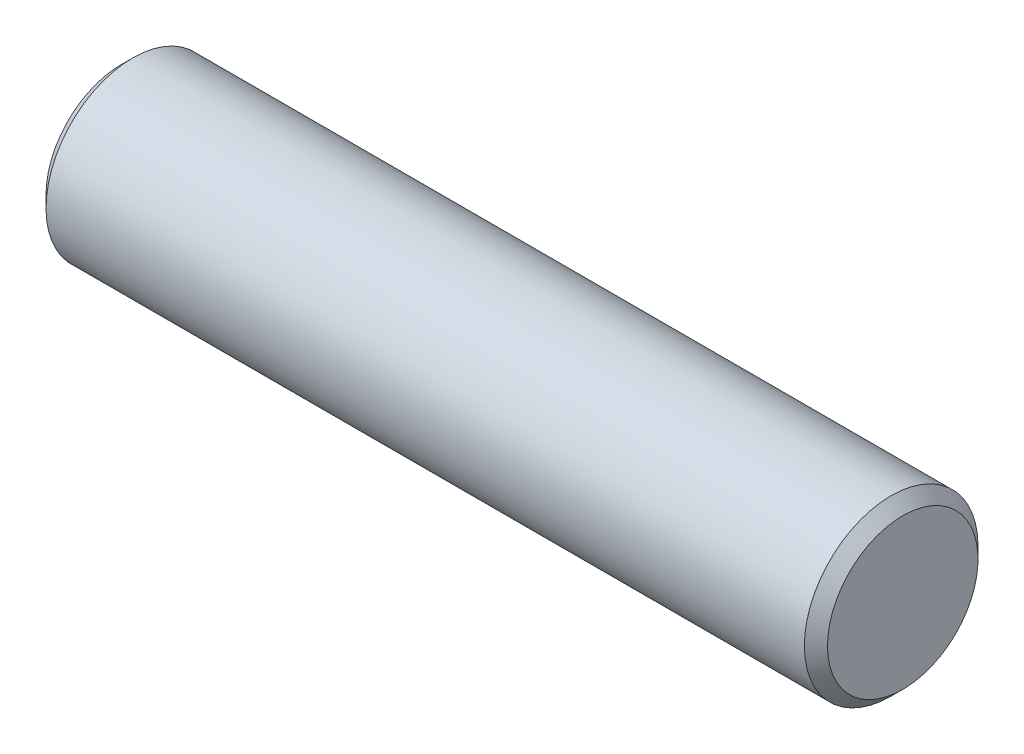
SolidWorks part; units mm, degrees
ref_plane "Front Plane" through (0, 0, 0) normal (0, 0, 1) x (1, 0, 0)
ref_plane "Top Plane" through (0, 0, 0) normal (0, 1, 0) x (1, 0, 0)
ref_plane "Right Plane" through (0, 0, 0) normal (1, 0, 0) x (0, 0, -1)
sketch "Эскиз1" plane through (0, 0, 0) normal (0, 0, 1) x (1, 0, 0)
  line L0 (0, 0) -> (103.8268, 0) construction
  line L1 (0, 0) -> (0, 1.3)
  line L2 (0.2, 1.5) -> (13.3, 1.5)
  line L3 (13.5, 1.3) -> (13.5, 0)
  line L4 (13.5, 0) -> (0, 0)
  line L5 (0, 1.3) -> (0.2, 1.5)
  line L6 (13.3, 1.5) -> (13.5, 1.3)
  point P4 (0, 1.5)
  point P5 (13.5, 1.5)
  dimension "D1" = 0.2
  dimension "D2" = 45
  dimension "D3" = 0.2
  dimension "D4" = 45
  dimension "D5" = 13.5
  dimension "D6" = 3
revolve "Повернуть1" add sketch "Эскиз1" angle 360 about L0
